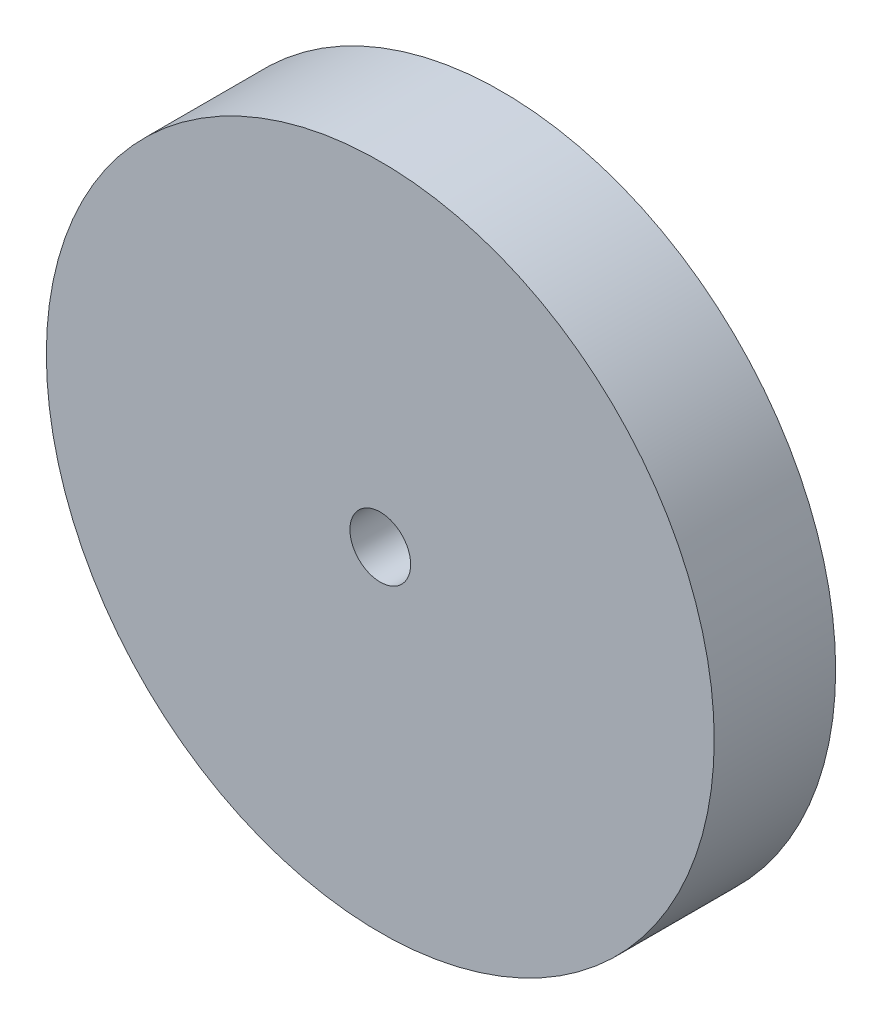
SolidWorks part; units mm, degrees
material "ABS"
ref_plane "前视基准面" through (0, 0, 0) normal (0, 0, 1) x (1, 0, 0)
ref_plane "上视基准面" through (0, 0, 0) normal (0, 1, 0) x (1, 0, 0)
ref_plane "右视基准面" through (0, 0, 0) normal (1, 0, 0) x (0, 0, -1)
other "Configuration Table"
sketch "草图1" plane through (0, 0, 0) normal (0, 0, 1) x (1, 0, 0)
  circle A0 centre (0, 0) radius 11
  dimension "D1" = 22
extrude "凸台-拉伸1" add sketch "草图1" along normal blind 4
sketch "草图2" plane through (0, 0, 4) normal (0, 0, 1) x (1, 0, 0)
  circle A0 centre (0, 0) radius 1
  dimension "D1" = 2
extrude "切除-拉伸1" cut sketch "草图2" against normal through all
